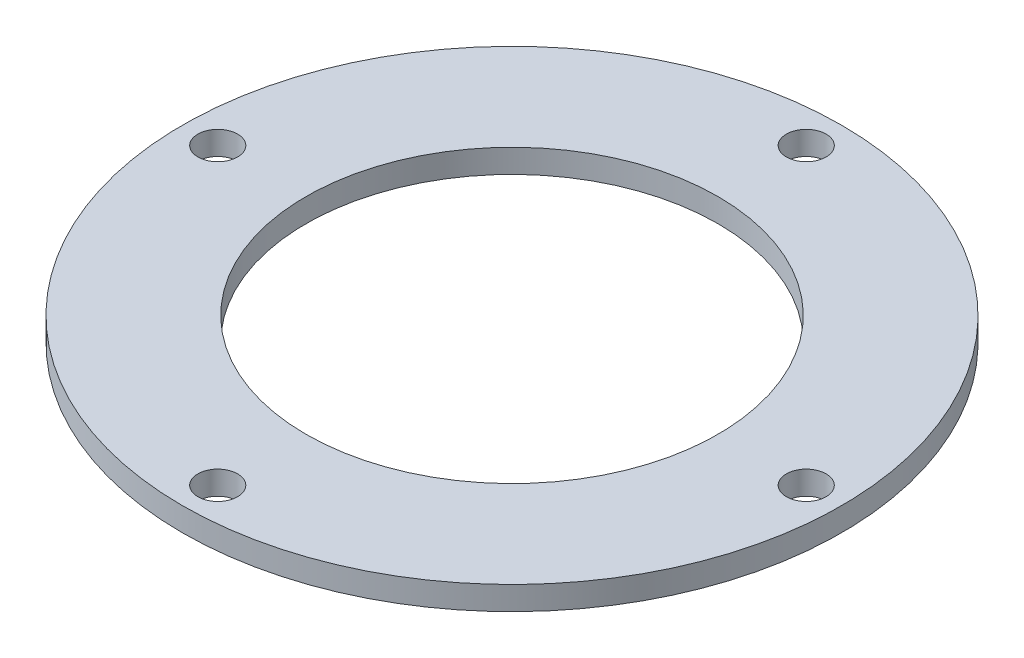
SolidWorks part; units mm, degrees
material "Acier non allié"
ref_plane "Plan de face" through (0, 0, 0) normal (0, 0, 1) x (1, 0, 0)
ref_plane "Plan de dessus" through (0, 0, 0) normal (0, 1, 0) x (1, 0, 0)
ref_plane "Plan de droite" through (0, 0, 0) normal (1, 0, 0) x (0, 0, -1)
sketch "Esquisse1" plane through (0, 0, 0) normal (0, 1, 0) x (1, 0, 0)
  circle A1 centre (0, 0) radius 35
  circle A2 centre (0, 50) radius 3.375
  circle A3 centre (0, 0) radius 56
  circle A4 centre (0, 0) radius 56
  circle A5 centre (50, 0) radius 3.375
  circle A6 centre (0, 0) radius 56
  circle A7 centre (0, -50) radius 3.375
  circle A8 centre (0, 0) radius 56
  circle A9 centre (-50, 0) radius 3.375
  point P18 (0, 0)
  dimension "D1" = 70
  dimension "D2" = 50
  dimension "D3" = 4
extrude "Boss.-Extru.1" add sketch "Esquisse1" along normal blind 4 contours A3 A9 A7 A5 A1 A2
